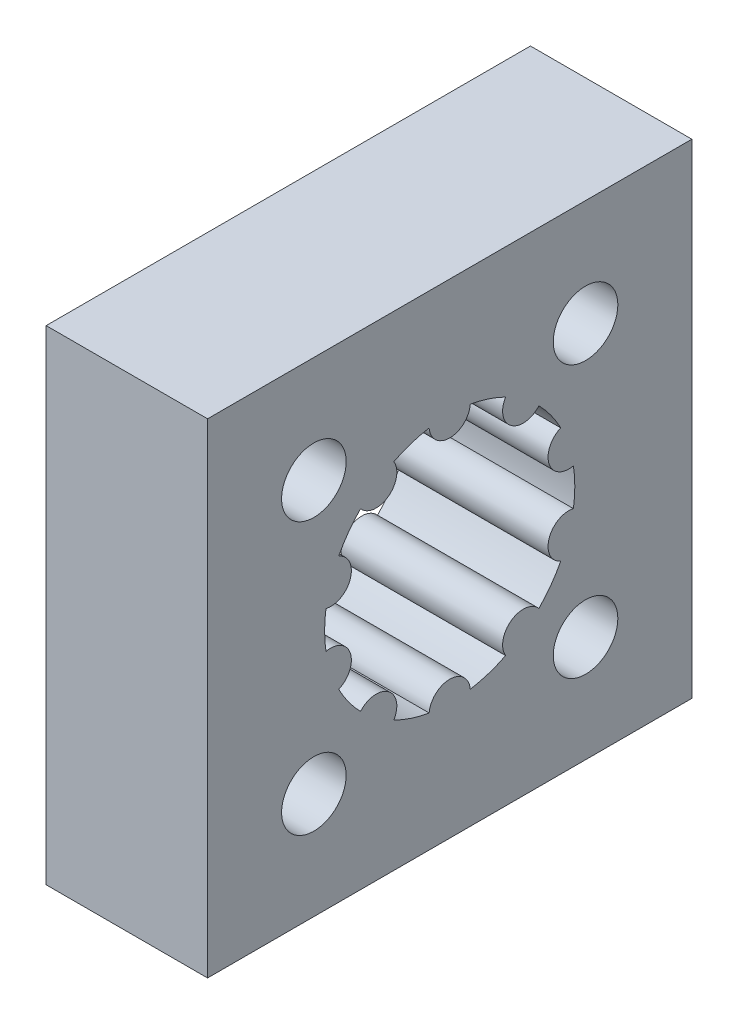
SolidWorks part; units mm, degrees
ref_plane "Front Plane" through (0, 0, 0) normal (0, 0, 1) x (1, 0, 0)
ref_plane "Top Plane" through (0, 0, 0) normal (0, 1, 0) x (1, 0, 0)
ref_plane "Right Plane" through (0, 0, 0) normal (1, 0, 0) x (0, 0, -1)
sketch "Sketch1" plane through (0, 0, 0) normal (1, 0, 0) x (0, 0, -1)
  line L0 (0, 0) -> (-1.2747, 7.6445) construction
  line L1 (0, 0) -> (1.2747, 7.6445) construction
  line L2 (0, 0) -> (3.4621, 6.9337) construction
  line L3 (0, 0) -> (0, 17.1645) construction
  line L4 (-1.2747, 7.6445) -> (1.2747, 7.6445) construction
  line L6 (-15, 15) -> (15, 15)
  line L7 (-15, 15) -> (-15, -15)
  line L8 (-15, -15) -> (15, -15)
  line L9 (15, 15) -> (15, -15)
  line L10 (-15, 15) -> (15, -15) construction
  line L11 (-15, -15) -> (15, 15) construction
  circle A0 centre (0, 0) radius 7.75 construction
  arc A2 (-1.2747, 7.6445) -> (1.2747, 7.6445) centre (0, 7.75) ccw
  arc A3 (1.2747, 7.6445) -> (3.4621, 6.9337) centre (0, 0) cw
  arc A4 (5.5245, 5.4353) -> (6.8764, 3.5745) centre (0, 0) cw
  arc A5 (3.4621, 6.9337) -> (5.5245, 5.4353) centre (4.5553, 6.2699) ccw
  arc A6 (7.6642, 1.15) -> (7.6642, -1.15) centre (0, 0) cw
  arc A7 (6.8764, 3.5745) -> (7.6642, 1.15) centre (7.3707, 2.3949) ccw
  arc A8 (6.8764, -3.5745) -> (5.5245, -5.4353) centre (0, 0) cw
  arc A9 (7.6642, -1.15) -> (6.8764, -3.5745) centre (7.3707, -2.3949) ccw
  arc A10 (3.4621, -6.9337) -> (1.2747, -7.6445) centre (0, 0) cw
  arc A11 (5.5245, -5.4353) -> (3.4621, -6.9337) centre (4.5553, -6.2699) ccw
  arc A12 (-1.2747, -7.6445) -> (-3.4621, -6.9337) centre (0, 0) cw
  arc A13 (1.2747, -7.6445) -> (-1.2747, -7.6445) centre (0, -7.75) ccw
  arc A14 (-5.5245, -5.4353) -> (-6.8764, -3.5745) centre (0, 0) cw
  arc A15 (-3.4621, -6.9337) -> (-5.5245, -5.4353) centre (-4.5553, -6.2699) ccw
  arc A16 (-7.6642, -1.15) -> (-7.6642, 1.15) centre (0, 0) cw
  arc A17 (-6.8764, -3.5745) -> (-7.6642, -1.15) centre (-7.3707, -2.3949) ccw
  arc A18 (-6.8764, 3.5745) -> (-5.5245, 5.4353) centre (0, 0) cw
  arc A19 (-7.6642, 1.15) -> (-6.8764, 3.5745) centre (-7.3707, 2.3949) ccw
  arc A20 (-3.4621, 6.9337) -> (-1.2747, 7.6445) centre (0, 0) cw
  arc A21 (-5.5245, 5.4353) -> (-3.4621, 6.9337) centre (-4.5553, 6.2699) ccw
  circle A22 centre (8.4146, 8.4146) radius 2
  circle A23 centre (8.4146, -8.4146) radius 2
  circle A24 centre (-8.4146, -8.4146) radius 2
  circle A25 centre (-8.4146, 8.4146) radius 2
  point P48 (0, 0)
  point P60 (0, 0)
  dimension "D1" = 15.5
  dimension "D2" = 10
  dimension "D6" = 4
  dimension "D7" = 11.9
  dimension "D3" = 36
  dimension "D4" = 2.3
  dimension "D5" = 30
  dimension "D8" = 4
extrude "Boss-Extrude1" add sketch "Sketch1" along normal blind 10 contours L9 L6 L7 L8 A18 A21 A20 A2 A3 A5 A4 A7 A6 A9 A8 A11 A10 A13 A12 A15 A14 A17 A16 A19
